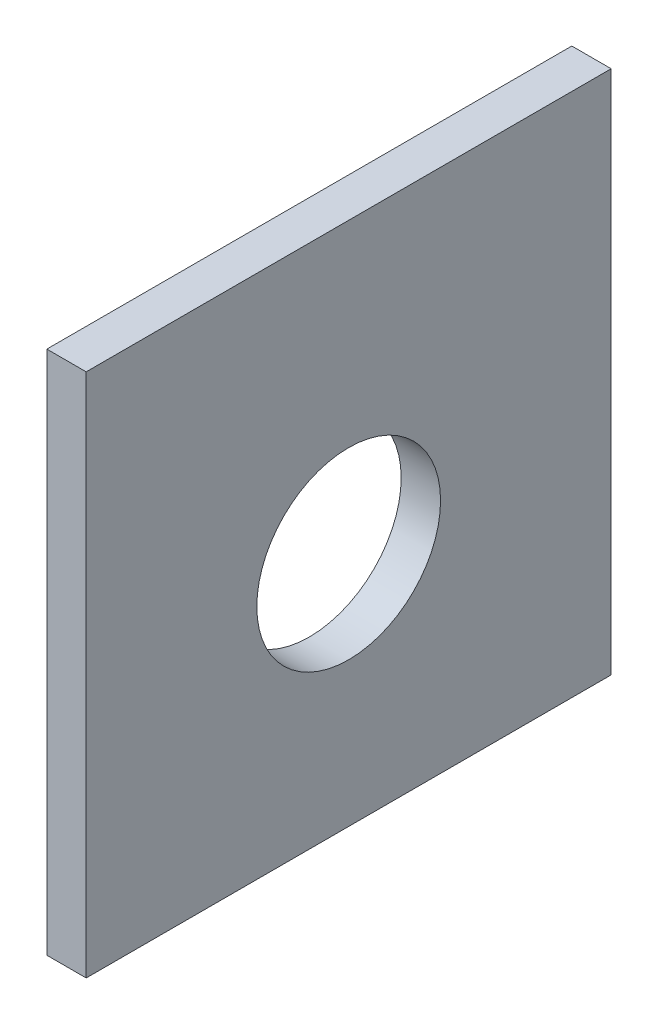
SolidWorks part; units mm, degrees
ref_plane "Alzado" through (0, 0, 0) normal (0, 0, 1) x (1, 0, 0)
ref_plane "Planta" through (0, 0, 0) normal (0, 1, 0) x (1, 0, 0)
ref_plane "Vista lateral" through (0, 0, 0) normal (1, 0, 0) x (0, 0, -1)
sketch "Croquis1" plane through (0, 0, 0) normal (1, 0, 0) x (0, 0, -1)
  line L0 (-31.2692, 7.8027) -> (8.7308, 7.8027)
  line L1 (8.7308, 7.8027) -> (8.7308, -32.1973)
  line L2 (8.7308, -32.1973) -> (-31.2692, -32.1973)
  line L3 (-31.2692, -32.1973) -> (-31.2692, 7.8027)
  circle A0 centre (-11.2692, -14.1973) radius 7
extrude "Saliente-Extruir1" add sketch "Croquis1" along normal blind 3
